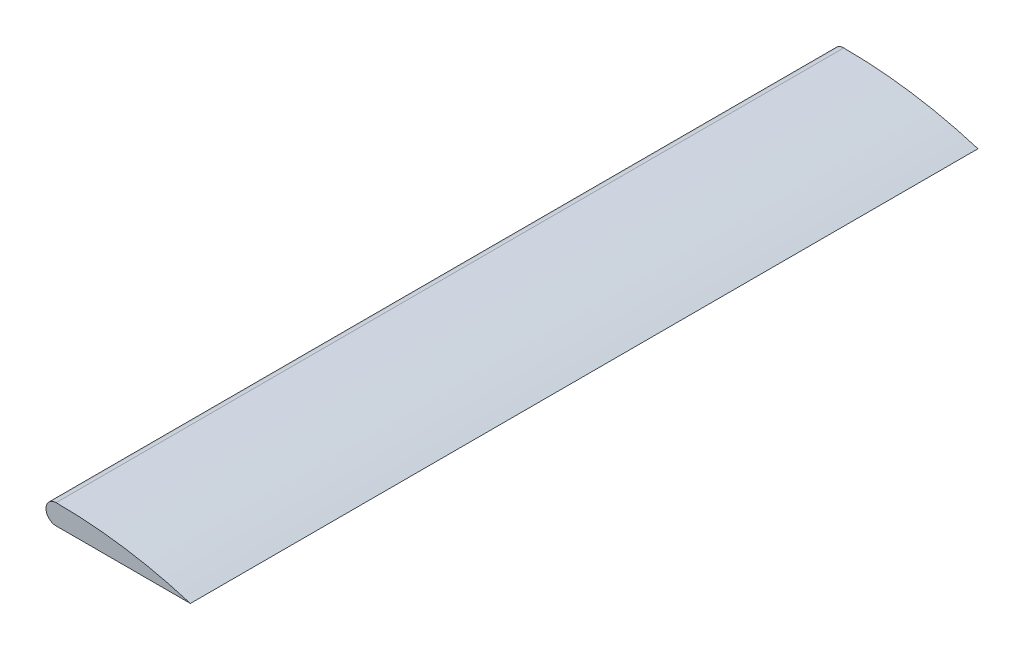
SolidWorks part; units mm, degrees
ref_plane "Front" through (0, 0, 0) normal (0, 0, 1) x (1, 0, 0)
ref_plane "Top" through (0, 0, 0) normal (0, 1, 0) x (1, 0, 0)
ref_plane "Right" through (0, 0, 0) normal (1, 0, 0) x (0, 0, -1)
sketch "Sketch1" plane through (0, 0, 0) normal (0, 0, 1) x (1, 0, 0)
  line L0 (0, 0) -> (204.6268, 0)
  line L1 (-15.3732, 15.3732) -> (204.6268, 15.3732) construction
  line L2 (204.6268, 15.3732) -> (204.6268, 0) construction
  arc A0 (0, 0) -> (0, 30.7463) centre (0, 15.3732) cw
  arc A1 (0, 30.7463) -> (204.6268, 0) centre (0, -665.5556) cw
  dimension "D1" = 220
extrude "Boss-Extrude1" add sketch "Sketch1" along normal blind 1200
